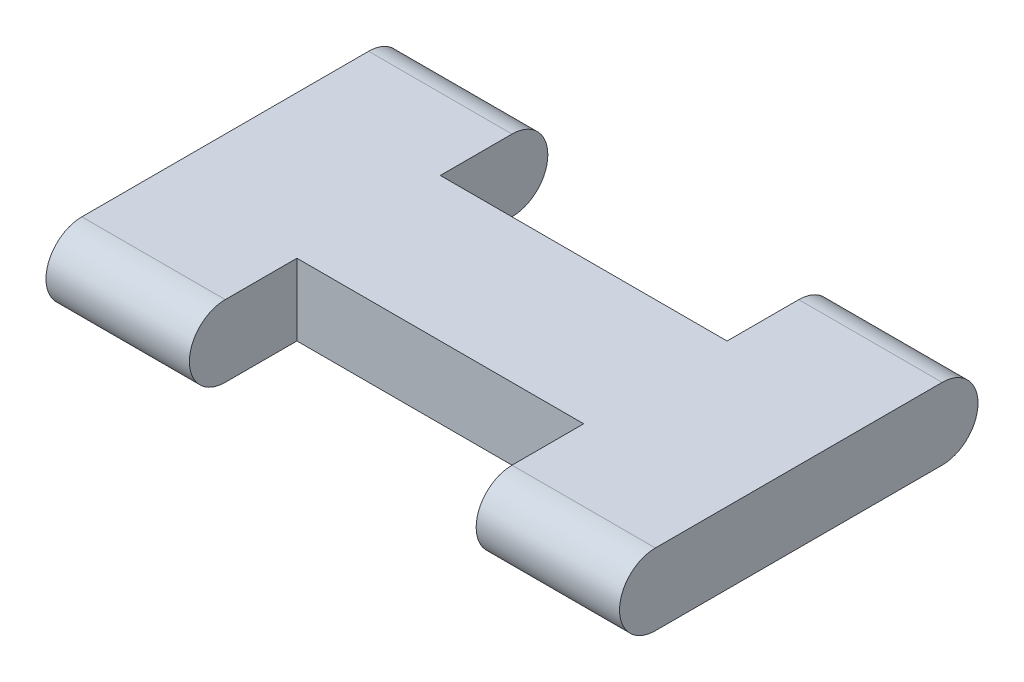
SolidWorks part; units mm, degrees
ref_plane "Front" through (0, 0, 0) normal (0, 0, 1) x (1, 0, 0)
ref_plane "Top" through (0, 0, 0) normal (0, 1, 0) x (1, 0, 0)
ref_plane "Right" through (0, 0, 0) normal (1, 0, 0) x (0, 0, -1)
sketch "草图1" plane through (0, 0, 0) normal (1, 0, 0) x (0, 0, -1)
  line L0 (-4, 0) -> (4, 0) construction
  line L1 (-4, 1) -> (4, 1)
  line L2 (-4, -1) -> (4, -1)
  arc A0 (-4, 1) -> (-4, -1) centre (-4, 0) ccw
  arc A1 (4, -1) -> (4, 1) centre (4, 0) ccw
  point P2 (0, 0)
extrude "凸台-拉伸1" add sketch "草图1" along normal blind 16
sketch "草图2" plane through (0, 1, 0) normal (0, 1, 0) x (1, 0, 0)
  line L0 (8, 5) -> (8, 2) construction
  line L1 (16, 5) -> (0, 5) construction
  line L2 (0, -5) -> (16, -5) construction
  line L3 (16, -4) -> (0, -4) construction
  line L4 (4, 11.7088) -> (12, 11.7088)
  line L5 (4, 11.7088) -> (4, 2)
  line L6 (4, -2) -> (12, -2)
  line L7 (12, 11.7088) -> (12, 2)
  line L8 (12, -11.6503) -> (4, -11.6503)
  line L9 (12, -11.6503) -> (12, -2)
  line L10 (12, 2) -> (4, 2)
  line L11 (4, -11.6503) -> (4, -2)
  line L12 (16, 4) -> (0, 4) construction
  line L13 (8, -2) -> (8, -5) construction
  dimension "D1" = 8
  dimension "D2" = 4
  dimension "D3" = 6
  dimension "D4" = 8
  dimension "D5" = 4
  dimension "D6" = 6
extrude "切除-拉伸1" cut sketch "草图2" against normal blind 14
